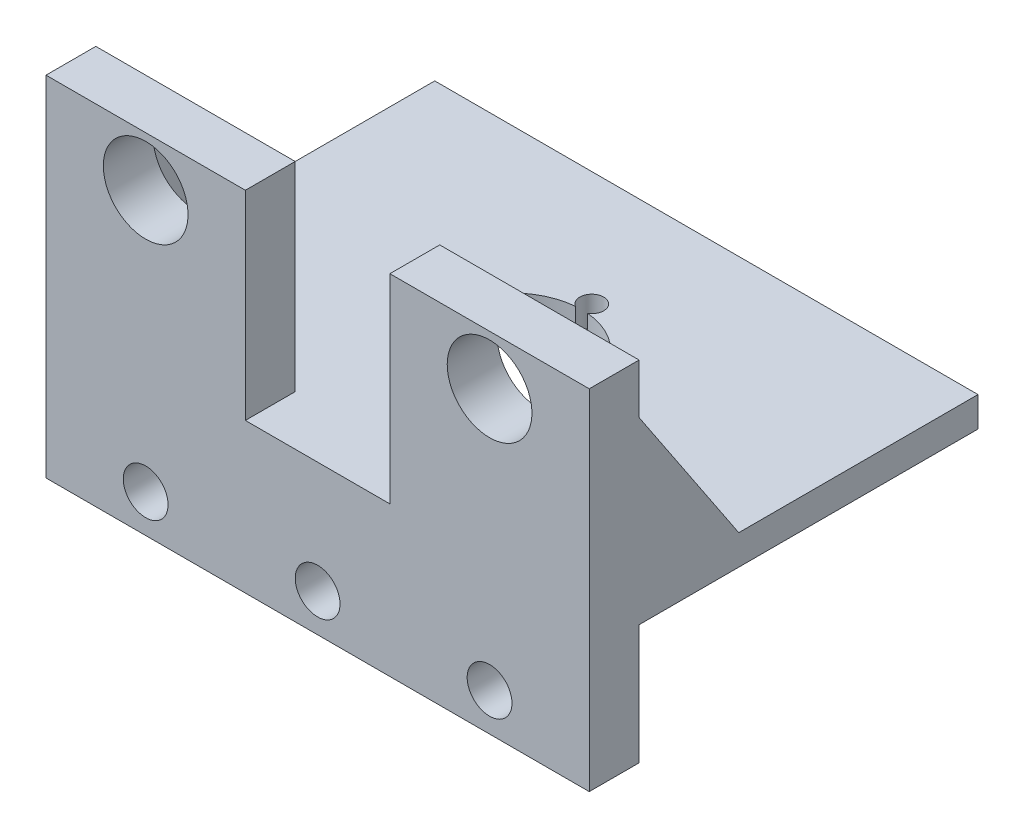
SolidWorks part; units mm, degrees
ref_plane "Front Plane" through (0, 0, 0) normal (0, 0, 1) x (1, 0, 0)
ref_plane "Top Plane" through (0, 0, 0) normal (0, 1, 0) x (1, 0, 0)
ref_plane "Right Plane" through (0, 0, 0) normal (1, 0, 0) x (0, 0, -1)
sketch "Sketch1" plane through (0, 0, 0) normal (0, 1, 0) x (1, 0, 0)
  line L1 (-40.6495, -11.3707) -> (13.8505, -11.3707)
  line L2 (-40.6495, -11.3707) -> (-40.6495, 27.6293)
  line L3 (-40.6495, 27.6293) -> (13.8505, 27.6293)
  line L4 (13.8505, -11.3707) -> (13.8505, 27.6293)
  dimension "D1" = 54.5
  dimension "D2" = 39
extrude "Boss-Extrude1" add sketch "Sketch1" along normal blind 3
sketch "Sketch10" plane through (0, 3, 0) normal (0, 1, 0) x (1, 0, 0)
  line L1 (13.8505, -11.3707) -> (13.8505, 27.6293) construction
  line L2 (-40.6495, -11.3707) -> (13.8505, -11.3707) construction
  circle A0 centre (-13.3995, 8.1293) radius 7
  dimension "D1" = 27.25
  dimension "D2" = 19.5
extrude "Cut-Extrude1" cut sketch "Sketch10" against normal blind 5 contours A0
hole_wizard "M2 Clearance Hole1" positions "3DSketch1" profile "Sketch11" hole size "M2" standard "ANSI Metric"
sketch3d "3DSketch1"
  line L0 (13.8505, 3, 11.3707) -> (13.8505, 3, -27.6293) construction
  line L1 (-40.6495, 3, 11.3707) -> (13.8505, 3, 11.3707) construction
  line L2 (-40.6495, 3, -27.6293) -> (-40.6495, 3, 11.3707) construction
  point P0 (-13.3995, 3, -0.1293)
  point P2 (-5.4048, 3, -8.1293)
  point P4 (-21.3943, 3, -8.1293)
  point P6 (-13.3995, 3, -16.1293)
  dimension "D1" = 16
  dimension "D2" = 11.31
  dimension "D3" = 11.31
  dimension "D4" = 11.31
  dimension "D5" = 11.31
  dimension "D6" = 27.25
  dimension "D7" = 27.25
  dimension "D8" = 11.5
  dimension "D9" = 19.2552
  dimension "D10" = 19.2552
sketch "Sketch11" plane through (-13.3995, 3, -0.1293) normal (1, 0, 0) x (0, 0, 1)
  line L0 (0, 0) -> (0, 17.721)
  line L1 (0, 17.721) -> (1.2, 17)
  line L2 (1.2, 17) -> (1.2, 0)
  line L5 (1.2, 0) -> (0, 0)
  line L10 (0, 17.721) -> (-1.2, 17) construction
  line L11 (0, -6.35) -> (0, 107.95) construction
  dimension "Hole Dia." = 2.4
  dimension "Hole Depth" = 17
  dimension "Drill Angle" = 118
sketch "Sketch12" plane through (0, 3, 0) normal (0, 1, 0) x (1, 0, 0)
  line L1 (13.8505, -11.3707) -> (-6.1495, -11.3707)
  line L2 (13.8505, -11.3707) -> (13.8505, -6.3707)
  line L3 (13.8505, -6.3707) -> (-6.1495, -6.3707)
  line L4 (-6.1495, -11.3707) -> (-6.1495, -6.3707)
  line L5 (-40.6495, -11.3707) -> (-20.6495, -11.3707)
  line L6 (-40.6495, -11.3707) -> (-40.6495, -6.3707)
  line L7 (-40.6495, -6.3707) -> (-20.6495, -6.3707)
  line L8 (-20.6495, -11.3707) -> (-20.6495, -6.3707)
  dimension "D1" = 20
  dimension "D2" = 20
  dimension "D3" = 5
  dimension "D4" = 5
extrude "Boss-Extrude2" add sketch "Sketch12" along normal blind 20
sketch "Sketch13" plane through (0, 0, 6.3707) normal (0, 0, -1) x (-1, 0, 0)
  line L1 (-13.8505, 23) -> (-13.8505, 3) construction
  line L2 (40.6495, 23) -> (40.6495, 3) construction
  line L3 (-13.8505, 3) -> (6.1495, 3) construction
  line L4 (20.6495, 3) -> (40.6495, 3) construction
  circle A0 centre (-3.8505, 18) radius 4.25
  circle A1 centre (30.6495, 18) radius 4.25
  dimension "D1" = 10
  dimension "D2" = 10
  dimension "D3" = 15
  dimension "D4" = 15
extrude "Cut-Extrude2" cut sketch "Sketch13" against normal blind 5
sketch "Sketch16" plane through (0, 0, 0) normal (0, -1, 0) x (1, 0, 0)
  line L0 (13.8505, 11.3707) -> (13.8505, -27.6293) construction
  line L1 (-40.6495, 11.3707) -> (13.8505, 11.3707)
  line L2 (-40.6495, 11.3707) -> (-40.6495, 6.3707)
  line L3 (-40.6495, 6.3707) -> (13.8505, 6.3707)
  line L4 (13.8505, 11.3707) -> (13.8505, 6.3707)
  dimension "D1" = 5
extrude "Boss-Extrude4" add sketch "Sketch16" along normal blind 12
hole_wizard "#8 Clearance Hole1" positions "3DSketch2" profile "Sketch17" hole size "#8" standard "ANSI Inch"
sketch3d "3DSketch2"
  line L1 (13.8505, 23, 11.3707) -> (13.8505, -12, 11.3707) construction
  line L2 (-40.6495, 23, 11.3707) -> (-40.6495, -12, 11.3707) construction
  line L4 (13.8505, -12, 11.3707) -> (-40.6495, -12, 11.3707) construction
  point P0 (-30.6495, -8.2, 11.3707)
  point P2 (-13.3995, -8.2, 11.3707)
  point P4 (3.8505, -8.2, 11.3707)
  dimension "D2" = 10
  dimension "D1" = 27.25
  dimension "D3" = 10
  dimension "D4" = 3.8
  dimension "D5" = 3.8
  dimension "D6" = 3.8
sketch "Sketch17" plane through (-30.6495, -8.2, 11.3707) normal (1, 0, 0) x (0, -1, 0)
  line L0 (0, 0) -> (0, 18.3507)
  line L1 (0, 18.3507) -> (2.2479, 17)
  line L2 (2.2479, 17) -> (2.2479, 0)
  line L5 (2.2479, 0) -> (0, 0)
  line L10 (0, 18.3507) -> (-2.2479, 17) construction
  line L11 (0, -6.35) -> (0, 107.95) construction
  dimension "Hole Dia." = 4.4958
  dimension "Hole Depth" = 17
  dimension "Drill Angle" = 118
sketch "Sketch20" plane through (13.8505, 0, 0) normal (1, 0, 0) x (0, 0, -1)
  line L0 (-6.3707, 18) -> (3.6293, 3)
  line L1 (-6.3707, 23) -> (-6.3707, 3) construction
  line L2 (-6.3707, 3) -> (27.6293, 3) construction
  dimension "D1" = 5
  dimension "D2" = 10
rib "Rib2" sketch "Sketch20" sketch "Sketch20" thickness 5 extrusion direction parallel to sketch draft on no parameters "D1"=5
sketch "Sketch21" plane through (-40.6495, 0, 0) normal (-1, 0, 0) x (0, 0, 1)
  line L0 (6.3707, 18) -> (-3.6293, 3)
  line L1 (6.3707, 23) -> (6.3707, 3) construction
  line L2 (-27.6293, 3) -> (6.3707, 3) construction
  dimension "D1" = 5
  dimension "D2" = 10
rib "Rib4" sketch "Sketch21" sketch "Sketch21" thickness 5 extrusion direction parallel to sketch draft on no parameters "D1"=5
